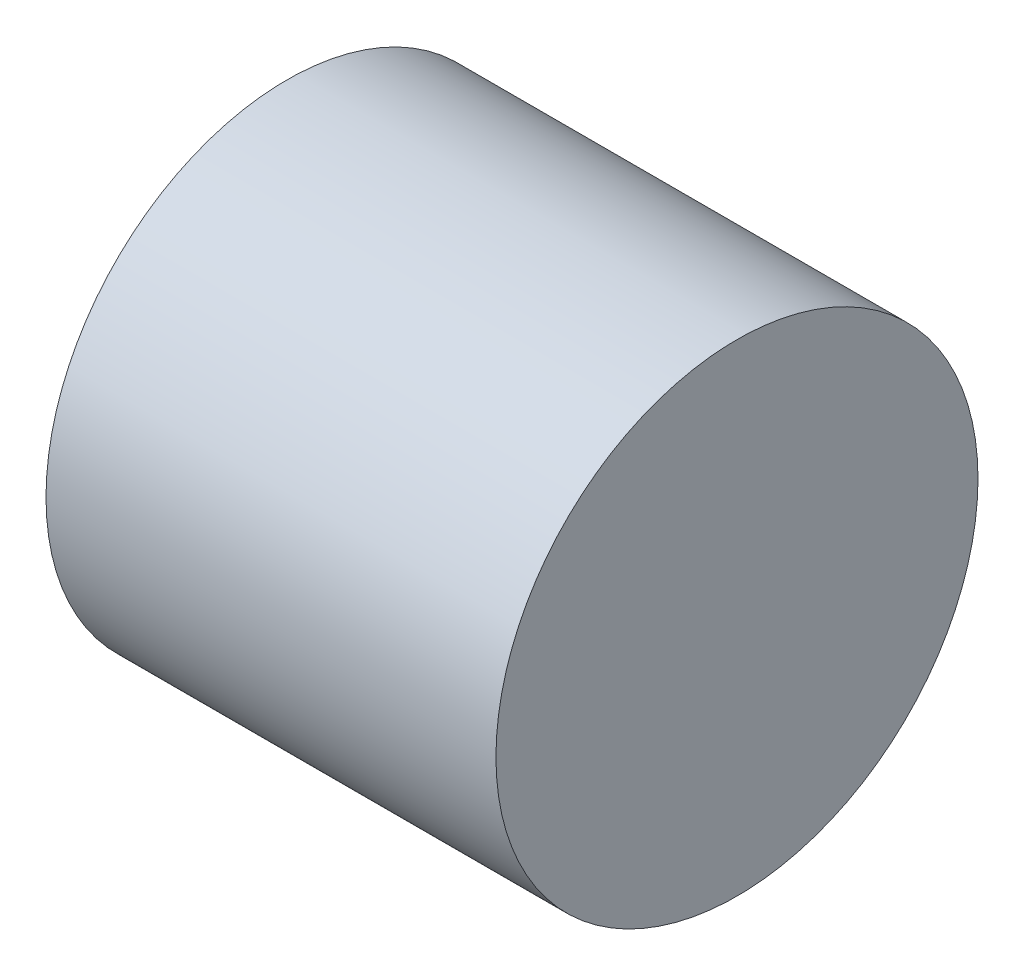
SolidWorks part; units mm, degrees
material "PBT General Purpose"
ref_plane "Front Plane" through (0, 0, 0) normal (0, 0, 1) x (1, 0, 0)
ref_plane "Top Plane" through (0, 0, 0) normal (0, 1, 0) x (1, 0, 0)
ref_plane "Right Plane" through (0, 0, 0) normal (1, 0, 0) x (0, 0, -1)
sketch "Sketch2" plane through (0, 0, 0) normal (0, 0, 1) x (1, 0, 0)
  line L0 (0, 0) -> (38.9655, 0) construction
  line L1 (0, 4) -> (0, 7.5)
  line L2 (0, 7.5) -> (14, 7.5)
  line L3 (14, 7.5) -> (14, 0)
  line L4 (0, 4) -> (10, 4)
  line L5 (10, 4) -> (12.3094, 0)
  line L6 (14, 0) -> (12.3094, 0)
  dimension "D1" = 7.5
  dimension "D2" = 14
  dimension "D3" = 4
  dimension "D4" = 10
  dimension "D5" = 60
revolve "Revolve1" add sketch "Sketch2" angle 360 about L0
